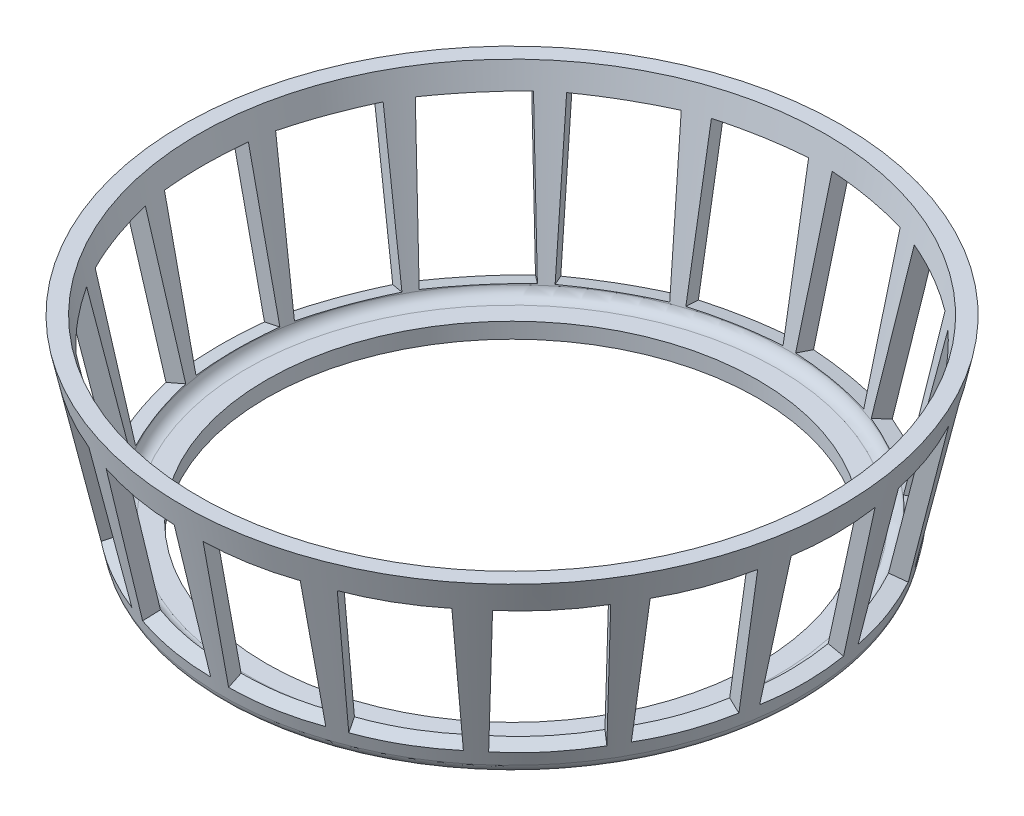
SolidWorks part; units mm, degrees
ref_plane "Front Plane" through (0, 0, 0) normal (0, 0, 1) x (1, 0, 0)
ref_plane "Top Plane" through (0, 0, 0) normal (0, 1, 0) x (1, 0, 0)
ref_plane "Right Plane" through (0, 0, 0) normal (1, 0, 0) x (0, 0, -1)
sketch "Sketch1" plane through (0, 0, 0) normal (0, 0, 1) x (1, 0, 0)
  line L0 (0, 0) -> (0, 12.339) construction
  line L1 (0, 0) -> (-24, 0) construction
  line L2 (-24.1702, 0.7892) -> (-27.5, 16.23)
  line L3 (-23.1927, 0) -> (-20.5, 0)
  line L4 (-22.1431, 1.3) -> (-20.5, 1.3)
  line L5 (-23.1207, 2.0892) -> (-26.1701, 16.23)
  line L6 (-20.5, 1.3) -> (-20.5, 0)
  line L7 (-27.5, 16.23) -> (-26.1701, 16.23)
  line L8 (-22.9505, 1.3) -> (-26.2292, 16.504) construction
  line L9 (-22.9505, 1.3) -> (-20.5, 1.3) construction
  arc A0 (-23.1927, 0) -> (-24.1702, 0.7892) centre (-23.1927, 1) cw
  arc A2 (-23.1207, 2.0892) -> (-22.1431, 1.3) centre (-22.1431, 2.3) ccw
  arc A3 (-22.9505, 1.3) -> (-22.9505, 1.3) centre (-22.9505, 1.3) cw construction
  dimension "D6" = 1
  dimension "D8" = 1
  dimension "D1" = 27.5
  dimension "D2" = 24
  dimension "D3" = 3.5
  dimension "D4" = 16.23
  dimension "D5" = 102.169
  dimension "D7" = 1.3
revolve "Revolve3" add sketch "Sketch1" angle 360 about L0
sketch "Sketch2" plane through (0, 0, 0) normal (0, 0, 1) x (1, 0, 0)
  line L0 (27.5, 16.23) -> (24.1702, 0.7892) construction
  line L1 (24.1702, 0.7892) -> (27.5, 16.23) construction
  arc A0 (23.1927, 0) -> (24.1702, 0.7892) centre (23.1927, 1) ccw construction
ref_plane "Plane1" through (22.9335, -4.9456, 0) normal (0.9775, -0.2108, 0) x (-0.2108, -0.9775, 0)
sketch "Sketch3" plane through (22.9335, -4.9456, 0) normal (0.9775, -0.2108, 0) x (-0.2108, -0.9775, 0)
  line L0 (0, 0) -> (-21.6624, 0) construction
  line L1 (-21.6624, 0) -> (-5.8666, 0) construction
  line L3 (-19.3124, -3.5) -> (-6.9624, -3.5)
  line L4 (-19.3124, -3.5) -> (-19.3124, 3.5)
  line L5 (-19.3124, 3.5) -> (-6.9624, 3.5)
  line L6 (-6.9624, -3.5) -> (-6.9624, 3.5)
  ellipse E0 centre (-15.8653, 0) end of major axis (-15.8653, -27.5) minor radius 5.7971 construction
  dimension "D1" = 7
  dimension "D2" = 12.35
  dimension "D3" = 2.35
extrude "Cut-Extrude1" cut sketch "Sketch3" against normal blind 10
pattern_circular "CirPattern1" count 18 over 360 about axis through (0, 0, 0) along (0, 1, 0) of "Cut-Extrude1"
